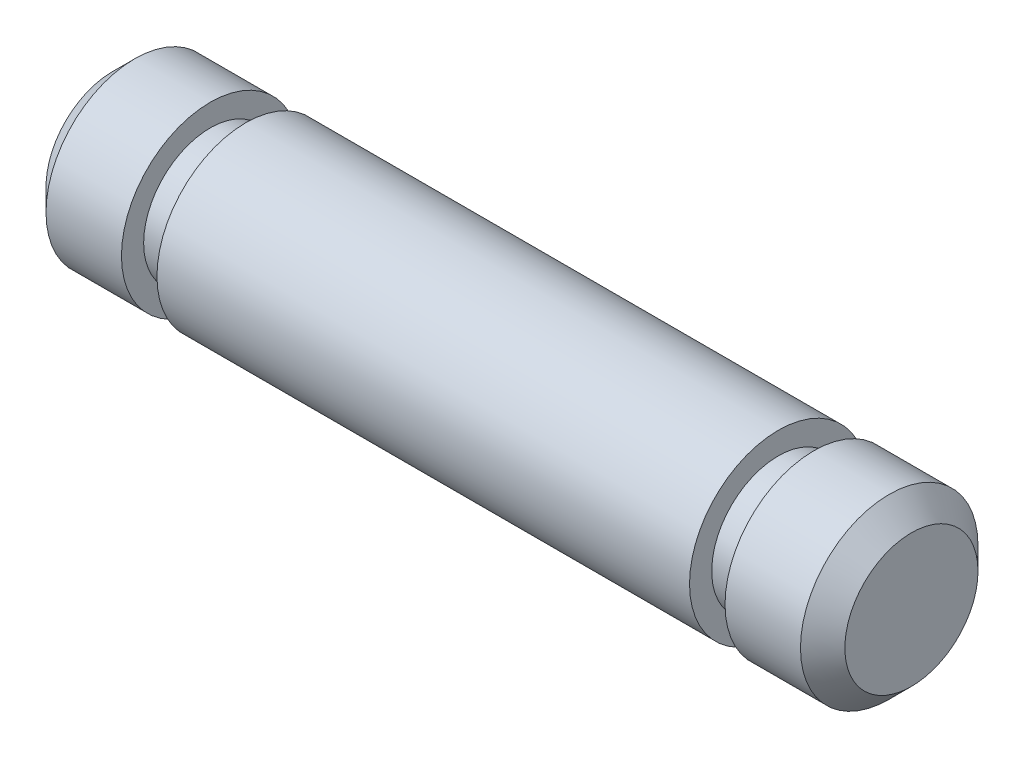
SolidWorks part; units mm, degrees
ref_plane "Front Plane" through (0, 0, 0) normal (0, 0, 1) x (1, 0, 0)
ref_plane "Top Plane" through (0, 0, 0) normal (0, 1, 0) x (1, 0, 0)
ref_plane "Right Plane" through (0, 0, 0) normal (1, 0, 0) x (0, 0, -1)
sketch "Sketch1" plane through (0, 0, 0) normal (1, 0, 0) x (0, 0, -1)
  circle A0 centre (0, 0) radius 2
extrude "Boss-Extrude1" add sketch "Sketch1" along normal blind 18
chamfer "Chamfer1" distance 0.5 angle 45 2 edges at (0, 0, -2) (18, 0, -2)
sketch "Sketch2" plane through (18, 0, 0) normal (1, 0, 0) x (0, 0, -1)
  circle A1 centre (0, 0) radius 1.5
  circle A2 centre (0, 0) radius 1.5
  circle A3 centre (0, 0) radius 2 construction
  circle A4 centre (0, 0) radius 2
  dimension "D1" = 0
extrude "Cut-Extrude1" cut sketch "Sketch2" along normal blind 0.8 from offset 3 offset against normal yes
sketch "Sketch3" plane through (0, 0, 0) normal (-1, 0, 0) x (0, 0, 1)
  circle A0 centre (0, 0) radius 2 construction
  circle A1 centre (0, 0) radius 1.5
  circle A2 centre (0, 0) radius 1.5
  circle A3 centre (0, 0) radius 2
  dimension "D1" = 0
extrude "Cut-Extrude2" cut sketch "Sketch3" along normal blind 0.8 from offset 3
